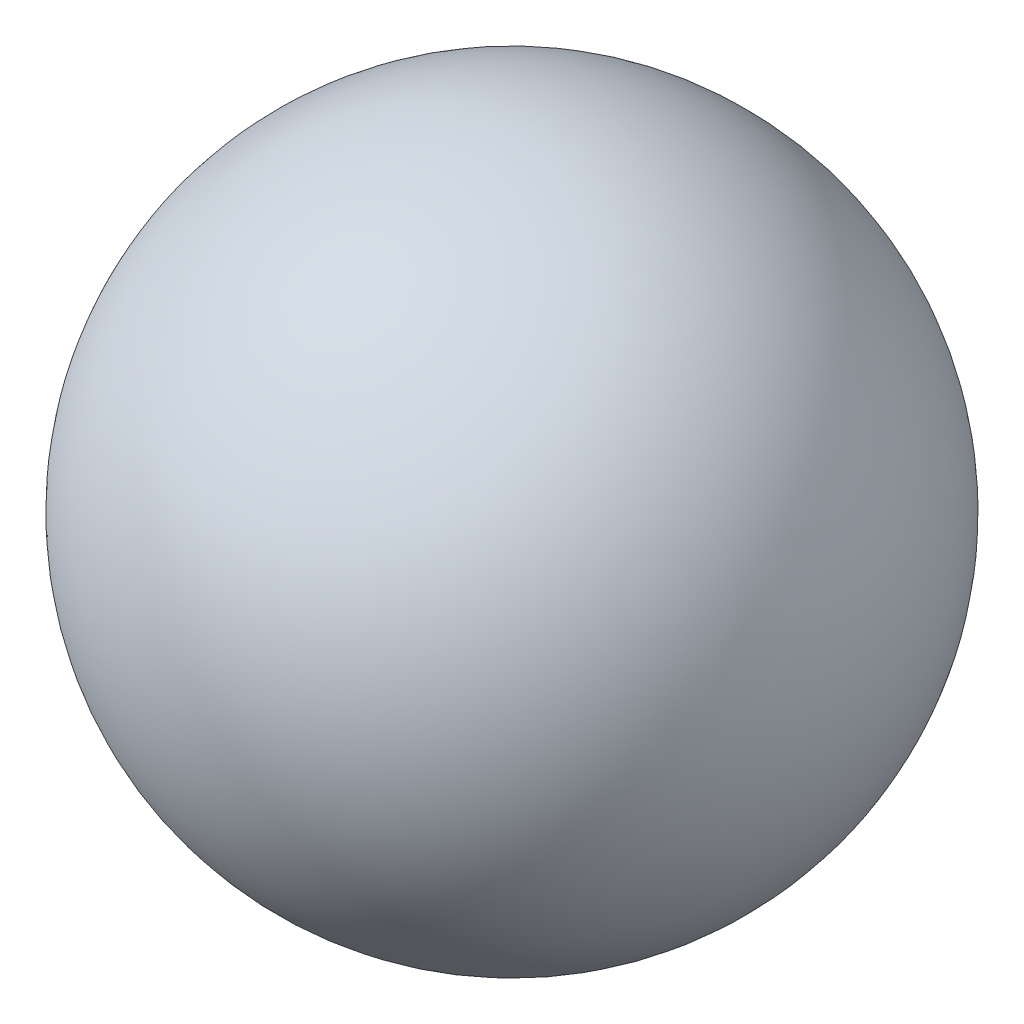
SolidWorks part; units mm, degrees
material "Titanium"
ref_plane "Front Plane" through (0, 0, 0) normal (0, 0, 1) x (1, 0, 0)
ref_plane "Top Plane" through (0, 0, 0) normal (0, 1, 0) x (1, 0, 0)
ref_plane "Right Plane" through (0, 0, 0) normal (1, 0, 0) x (0, 0, -1)
sketch "Sketch1" plane through (0, 0, 0) normal (0, 1, 0) x (1, 0, 0)
  line L0 (0, 0) -> (-550, 0)
  arc A0 (-550, 0) -> (0, 0) centre (-275, 0) cw
  dimension "D2" = 275
  dimension "D1" = 550
revolve "Revolve1" add sketch "Sketch1" angle 360 about L0
